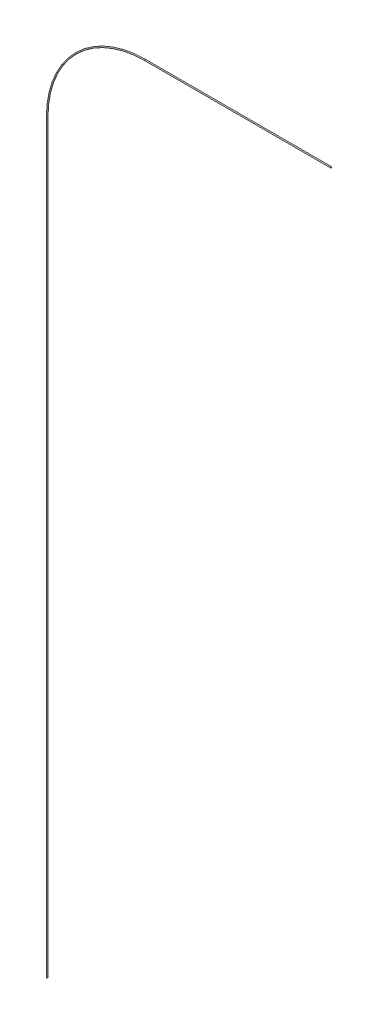
SolidWorks part; units mm, degrees
ref_plane "Front Plane" through (0, 0, 0) normal (0, 0, 1) x (1, 0, 0)
ref_plane "Top Plane" through (0, 0, 0) normal (0, 1, 0) x (1, 0, 0)
ref_plane "Right Plane" through (0, 0, 0) normal (1, 0, 0) x (0, 0, -1)
sketch "Sketch1" plane through (0, 0, 0) normal (0, 0, 1) x (1, 0, 0)
  line L2 (32.3357, 96.1081) -> (-9.9465, 96.1081)
  line L3 (-32.3357, 73.7188) -> (-32.3357, -96.1081)
  arc A0 (-9.9465, 96.1081) -> (-32.3357, 73.7188) centre (-9.9465, 73.7188) ccw
ref_plane "Plane2" through (32.3357, 0, 0) normal (1, 0, 0) x (0, 0, -1)
sweep "Sweep3" add path "Sketch1" circular profile diameter 0.254 parameters "D3"=0.254
